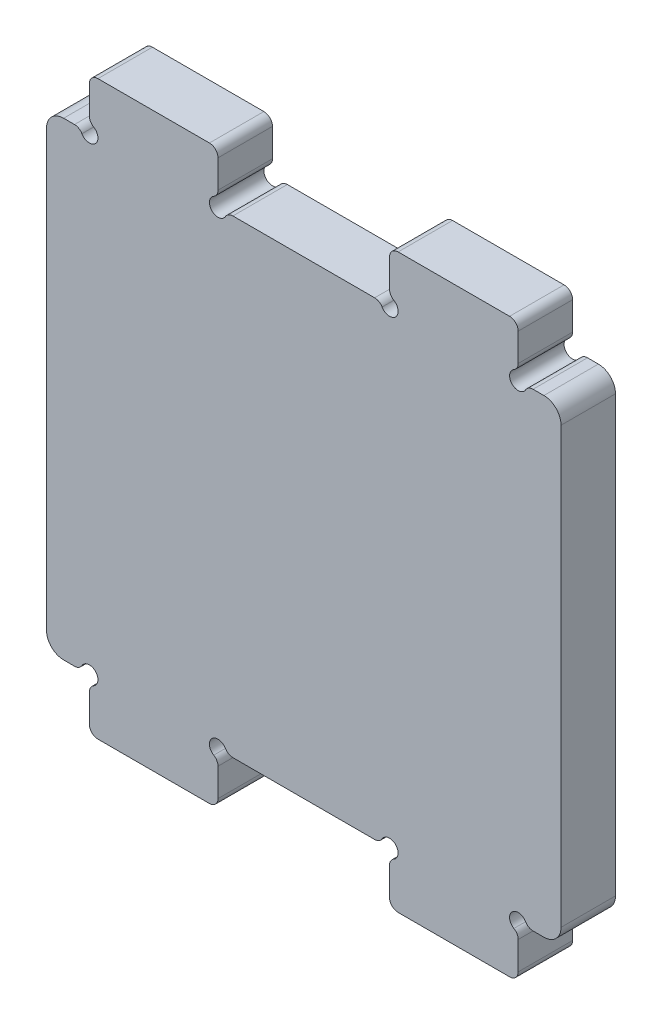
SolidWorks part; units mm, degrees
ref_plane "Front Plane" through (0, 0, 0) normal (0, 0, 1) x (1, 0, 0)
ref_plane "Top Plane" through (0, 0, 0) normal (0, 1, 0) x (1, 0, 0)
ref_plane "Right Plane" through (0, 0, 0) normal (1, 0, 0) x (0, 0, -1)
sketch "Sketch1" plane through (0, 0, 0) normal (0, 0, 1) x (1, 0, 0)
  line L0 (-30, 27.35) -> (30, 27.35)
  line L1 (-30, 27.35) -> (-30, -27.35)
  line L2 (30, 27.35) -> (30, -27.35)
  line L3 (-30, -27.35) -> (30, -27.35)
  line L4 (30, -27.35) -> (-30, 27.35) construction
  point P0 (0, 0)
  dimension "D1" = 60
  dimension "D2" = 54.7
extrude "Boss-Extrude1" add sketch "Sketch1" along normal blind 6.35
sketch "Sketch2" plane through (0, 0, 6.35) normal (0, 0, 1) x (1, 0, 0)
  line L0 (-25, 27.35) -> (-10, 27.35)
  line L1 (-25, 27.35) -> (-25, 33.35)
  line L2 (-10, 27.35) -> (-10, 33.35)
  line L3 (-25, 33.35) -> (-10, 33.35)
  line L4 (30, 27.35) -> (-30, 27.35) construction
  line L5 (-30, 27.35) -> (-30, -27.35) construction
  dimension "D1" = 5
  dimension "D2" = 15
  dimension "D3" = 6
extrude "Boss-Extrude2" add sketch "Sketch2" against normal up to surface (6.35 mm away) up to face at (0, 0, 0)
sketch "Sketch3" plane through (0, 0, 6.35) normal (0, 0, 1) x (1, 0, 0)
  circle A0 centre (-25, 27.35) radius 1
  circle A1 centre (-10, 27.35) radius 1
  dimension "D1" = 2
extrude "Cut-Extrude1" cut sketch "Sketch3" against normal through all
mirror "Mirror1" about plane through (0, 0, 0) normal (1, 0, 0) of "Boss-Extrude2", "Cut-Extrude1"
mirror "Mirror2" about plane through (0, 0, 0) normal (0, 1, 0) of "Mirror1", "Boss-Extrude2", "Cut-Extrude1"
fillet "Fillet1" radius 1 24 edges at (26, -27.35, 3.175) (25, -28.35, 3.175) (25, -33.35, 3.175) (10, -33.35, 3.175) (10, -28.35, 3.175) (9, -27.35, 3.175) (-9, -27.35, 3.175) (-10, -28.35, 3.175) (-10, -33.35, 3.175) (-25, -33.35, 3.175) (-25, -28.35, 3.175) (-26, -27.35, 3.175) (26, 27.35, 3.175) (25, 28.35, 3.175) (25, 33.35, 3.175) (10, 33.35, 3.175) (10, 28.35, 3.175) (9, 27.35, 3.175) (-9, 27.35, 3.175) (-10, 28.35, 3.175) (-10, 33.35, 3.175) (-25, 33.35, 3.175) (-25, 28.35, 3.175) (-26, 27.35, 3.175)
fillet "Fillet2" radius 2 4 edges at (30, -27.35, 3.175) (30, 27.35, 3.175) (-30, -27.35, 3.175) (-30, 27.35, 3.175)
